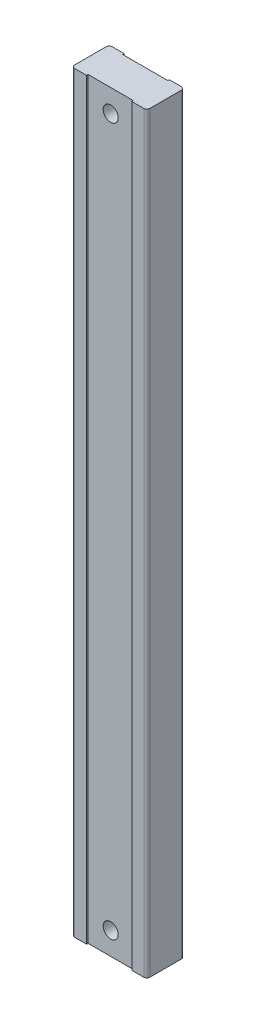
SolidWorks part; units mm, degrees
ref_plane "Front Plane" through (0, 0, 0) normal (0, 0, 1) x (1, 0, 0)
ref_plane "Top Plane" through (0, 0, 0) normal (0, 1, 0) x (1, 0, 0)
ref_plane "Right Plane" through (0, 0, 0) normal (1, 0, 0) x (0, 0, -1)
sketch "Sketch1" plane through (0, 0, 0) normal (0, 1, 0) x (1, 0, 0)
  line L1 (-73.9039, 1.6909) -> (-27.9039, 1.6909)
  line L2 (-75.9039, -0.3091) -> (-75.9039, -21.3091)
  line L3 (-73.9039, -23.3091) -> (-27.9039, -23.3091)
  line L4 (-25.9039, -0.3091) -> (-25.9039, -21.3091)
  arc A0 (-73.9039, -23.3091) -> (-75.9039, -21.3091) centre (-73.9039, -21.3091) cw
  arc A1 (-25.9039, -21.3091) -> (-27.9039, -23.3091) centre (-27.9039, -21.3091) cw
  arc A2 (-27.9039, 1.6909) -> (-25.9039, -0.3091) centre (-27.9039, -0.3091) cw
  arc A3 (-73.9039, 1.6909) -> (-75.9039, -0.3091) centre (-73.9039, -0.3091) ccw
  dimension "D1" = 2
extrude "Boss-Extrude1" add sketch "Sketch1" along normal blind 500
ref_plane "Plane1" through (0, 500, 0) normal (0, 1, 0) x (1, 0, 0)
sketch "Sketch3" plane through (0, 500, 0) normal (0, 1, 0) x (1, 0, 0)
  line L0 (-27.9039, 1.6909) -> (-73.9039, 1.6909) construction
  line L1 (-65.9039, 1.6909) -> (-35.9039, 1.6909)
  line L2 (-65.9039, 1.6909) -> (-65.9039, 0.6909)
  line L3 (-65.9039, 0.6909) -> (-35.9039, 0.6909)
  line L4 (-35.9039, 1.6909) -> (-35.9039, 0.6909)
  line L5 (-73.9039, -23.3091) -> (-27.9039, -23.3091) construction
  line L6 (-65.9039, -23.3091) -> (-35.9039, -23.3091)
  line L7 (-65.9039, -23.3091) -> (-65.9039, -22.3091)
  line L8 (-65.9039, -22.3091) -> (-35.9039, -22.3091)
  line L9 (-35.9039, -23.3091) -> (-35.9039, -22.3091)
  line L10 (-25.9039, -21.3091) -> (-25.9039, -0.3091) construction
  line L11 (-75.9039, -0.3091) -> (-75.9039, -21.3091) construction
  dimension "D1" = 1
  dimension "D2" = 1
  dimension "D3" = 10
  dimension "D4" = 10
  dimension "D5" = 10
  dimension "D6" = 10
extrude "Cut-Extrude1" cut sketch "Sketch3" against normal blind 500
ref_plane "Plane2" through (0, 0, 22.3091) normal (0, 0, 1) x (1, 0, 0)
sketch "Sketch4" plane through (0, 0, 22.3091) normal (0, 0, 1) x (1, 0, 0)
  line L0 (-35.9039, 0) -> (-65.9039, 0) construction
  line L1 (-75.9039, 500) -> (-75.9039, 0) construction
  line L2 (19.25, 500) -> (-19.25, 500) construction
  point P0 (-50.9039, 15)
  point P1 (-50.9039, 0)
  point P6 (-50.9039, 485)
  dimension "D1" = 15
  dimension "D2" = 25
  dimension "D3" = 15
  dimension "D4" = 25
hole_wizard "M10x1.0 Tapped Hole1" positions "3DSketch1" profile "Sketch5" tap size "M10x1.0" standard "ANSI Metric"
sketch3d "3DSketch1"
  point P0 (-50.9039, 485, 22.3091)
  point P3 (-50.9039, 15, 22.3091)
sketch "Sketch5" plane through (-50.9039, 485, 22.3091) normal (1, 0, 0) x (0, -1, 0)
  line L0 (0, 0) -> (0, 53.9639)
  line L1 (0, 53.9639) -> (4.5, 51.26)
  line L2 (4.5, 51.26) -> (4.5, 45.4)
  line L3 (4.5, 45.4) -> (5, 45.4)
  line L4 (5, 45.4) -> (5, 0)
  line L5 (5, 0) -> (0, 0)
  line L10 (0, 53.9639) -> (-4.5, 51.26) construction
  line L11 (0, -6.35) -> (0, 107.95) construction
  dimension "Tap Drill Dia." = 9
  dimension "Tap Drill Depth" = 51.26
  dimension "Thread Major Dia." = 10
  dimension "Thread Depth" = 45.4
  dimension "Drill Angle" = 118
